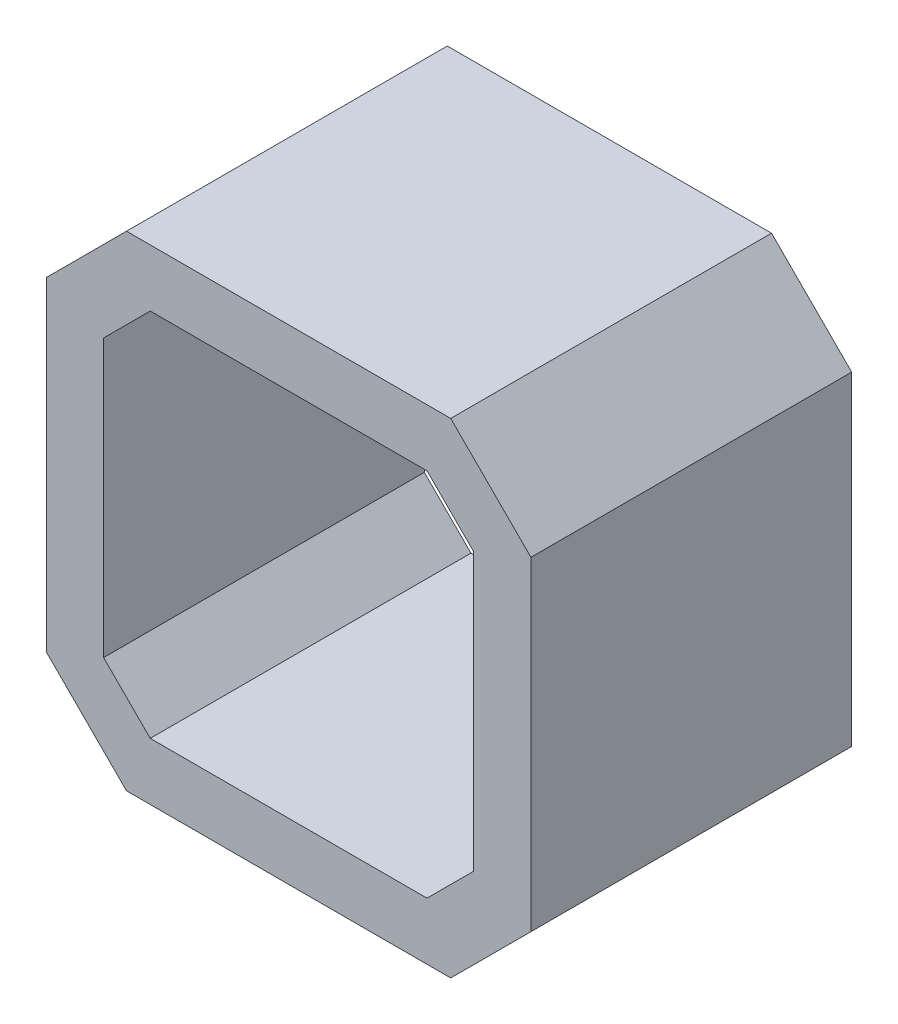
SolidWorks part; units mm, degrees
ref_plane "Front Plane" through (0, 0, 0) normal (0, 0, 1) x (1, 0, 0)
ref_plane "Top Plane" through (0, 0, 0) normal (0, 1, 0) x (1, 0, 0)
ref_plane "Right Plane" through (0, 0, 0) normal (1, 0, 0) x (0, 0, -1)
sketch "Sketch1" plane through (0, 0, 0) normal (0, 0, 1) x (1, 0, 0)
  line L0 (-21.15, 14.15) -> (-14.15, 21.15)
  line L1 (-14.15, -21.15) -> (14.15, -21.15)
  line L2 (-21.15, -14.15) -> (-21.15, 14.15)
  line L3 (-14.15, 21.15) -> (14.15, 21.15)
  line L4 (21.15, -14.15) -> (21.15, 14.15)
  line L5 (-21.15, -21.15) -> (21.15, 21.15) construction
  line L6 (-21.15, 21.15) -> (21.15, -21.15) construction
  line L7 (14.15, 21.15) -> (21.15, 14.15)
  line L8 (14.15, -21.15) -> (21.15, -14.15)
  line L9 (-21.15, -14.15) -> (-14.15, -21.15)
  line L10 (-12.0789, 16.15) -> (12.0789, 16.15)
  line L11 (12.0789, 16.15) -> (16.15, 12.0789)
  line L12 (16.15, -12.0789) -> (16.15, 12.0789)
  line L13 (12.0789, -16.15) -> (16.15, -12.0789)
  line L14 (-12.0789, -16.15) -> (12.0789, -16.15)
  line L15 (-16.15, -12.0789) -> (-12.0789, -16.15)
  line L16 (-16.15, -12.0789) -> (-16.15, 12.0789)
  line L17 (-16.15, 12.0789) -> (-12.0789, 16.15)
  point P0 (0, 0)
  dimension "D1" = 42.3
  dimension "D2" = 42.3
  dimension "D3" = 5
extrude "Body" add sketch "Sketch1" along normal blind 28
